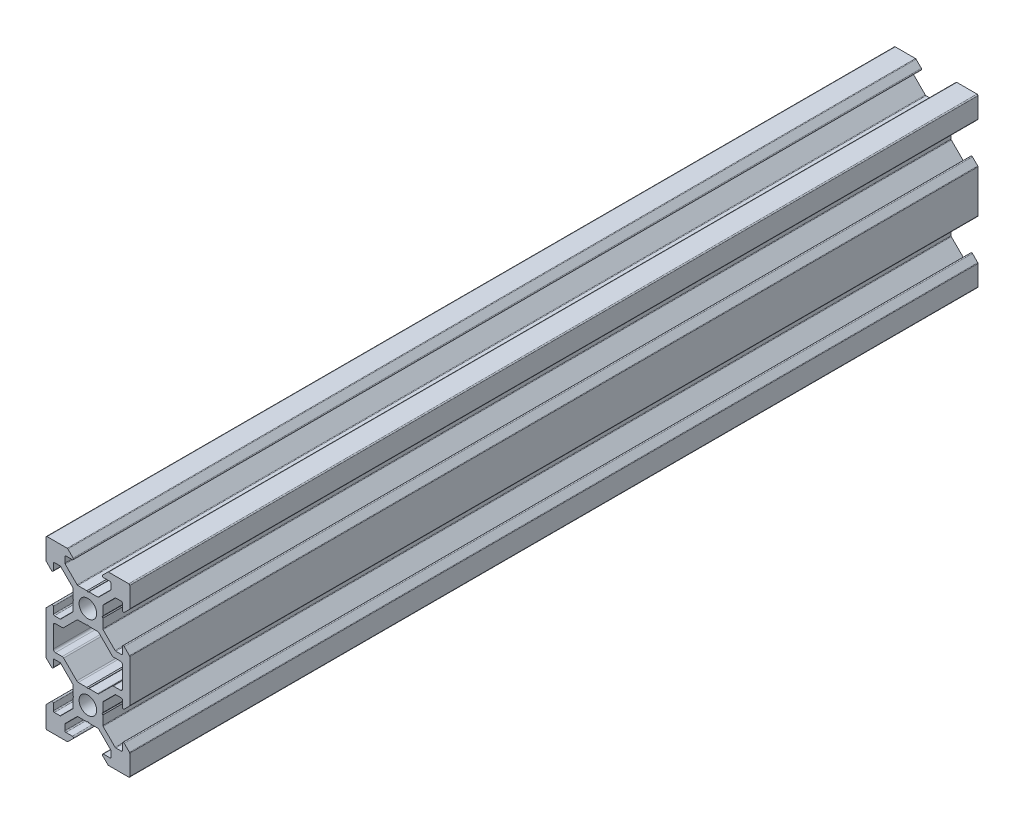
SolidWorks part; units mm, degrees
ref_plane "Front Plane" through (0, 0, 0) normal (0, 0, 1) x (1, 0, 0)
ref_plane "Top Plane" through (0, 0, 0) normal (0, 1, 0) x (1, 0, 0)
ref_plane "Right Plane" through (0, 0, 0) normal (1, 0, 0) x (0, 0, -1)
sketch "Sketch1" plane through (0, 0, 0) normal (0, 0, 1) x (1, 0, 0)
  line L0 (3.5607, 3.5607) -> (10.6317, 10.6317) construction
  line L1 (2.5, -3.5607) -> (-2.5, -3.5607)
  line L2 (3.5607, -2.5) -> (3.5607, 2.5)
  line L3 (2.5, 3.5607) -> (-2.5, 3.5607)
  line L4 (-3.5607, -2.5) -> (-3.5607, 2.5)
  line L5 (3.5607, -3.5607) -> (-3.5607, 3.5607) construction
  line L6 (3.5607, 3.5607) -> (-3.5607, -3.5607) construction
  line L7 (2.5, 3.5607) -> (5.5, 6.5607)
  line L8 (5.5, 6.5607) -> (5.5, 8.2521)
  line L9 (5.5, 8.2521) -> (3.1, 8.2521)
  line L10 (3.1, 8.2521) -> (4.8479, 10)
  line L11 (4.8479, 10) -> (10, 10)
  line L12 (3.5607, 2.5) -> (6.5607, 5.5)
  line L13 (6.5607, 5.5) -> (8.2521, 5.5)
  line L14 (8.2521, 5.5) -> (8.2521, 3.1)
  line L15 (8.2521, 3.1) -> (10, 4.8479)
  line L16 (10, 4.8479) -> (10, 10)
  line L17 (0, -55) -> (0, 55) construction
  line L18 (-3.5607, 3.5607) -> (-10.6317, 10.6317) construction
  line L19 (-10, 4.8479) -> (-10, 10)
  line L20 (-8.2521, 3.1) -> (-10, 4.8479)
  line L21 (-8.2521, 5.5) -> (-8.2521, 3.1)
  line L22 (-6.5607, 5.5) -> (-8.2521, 5.5)
  line L23 (-3.5607, 2.5) -> (-6.5607, 5.5)
  line L24 (-4.8479, 10) -> (-10, 10)
  line L25 (-3.1, 8.2521) -> (-4.8479, 10)
  line L26 (-5.5, 8.2521) -> (-3.1, 8.2521)
  line L27 (-5.5, 6.5607) -> (-5.5, 8.2521)
  line L28 (-2.5, 3.5607) -> (-5.5, 6.5607)
  line L29 (-8.2521, -7) -> (-5.9393, -7)
  line L30 (55, 0) -> (-55, 0) construction
  line L31 (-3.5607, -3.5607) -> (-10.6317, -10.6317) construction
  line L32 (3.5607, -3.5607) -> (10.6317, -10.6317) construction
  line L33 (-2.5, -3.5607) -> (-5.5, -6.5607)
  line L34 (-5.5, -6.5607) -> (-5.9393, -7)
  line L35 (5.5, -6.5607) -> (5.9393, -7)
  line L36 (8.2521, -7) -> (5.9393, -7)
  line L37 (-12.2633, -10) -> (14.5346, -10) construction
  line L38 (-3.5607, -2.5) -> (-6.5607, -5.5)
  line L39 (-6.5607, -5.5) -> (-8.2521, -5.5)
  line L40 (-8.2521, -5.5) -> (-8.2521, -3.1)
  line L41 (-8.2521, -3.1) -> (-10, -4.8479)
  line L42 (-10, -4.8479) -> (-10, -7)
  line L43 (10, -4.8479) -> (10, -7)
  line L44 (8.2521, -3.1) -> (10, -4.8479)
  line L45 (8.2521, -5.5) -> (8.2521, -3.1)
  line L46 (6.5607, -5.5) -> (8.2521, -5.5)
  line L47 (3.5607, -2.5) -> (6.5607, -5.5)
  line L48 (-3.5607, -23.5607) -> (-10.6317, -30.6317) construction
  line L49 (3.5607, -23.5607) -> (-3.5607, -16.4393) construction
  line L50 (3.5607, -16.4393) -> (-3.5607, -23.5607) construction
  line L51 (3.5607, -23.5607) -> (10.6317, -30.6317) construction
  line L52 (2.5, -3.5607) -> (5.5, -6.5607)
  line L53 (2.5, -16.4393) -> (5.5, -13.4393)
  line L54 (3.5607, -17.5) -> (6.5607, -14.5)
  line L55 (6.5607, -14.5) -> (8.2521, -14.5)
  line L56 (8.2521, -14.5) -> (8.2521, -16.9)
  line L57 (8.2521, -16.9) -> (10, -15.1521)
  line L58 (10, -15.1521) -> (10, -13)
  line L59 (-10, -15.1521) -> (-10, -13)
  line L60 (-8.2521, -16.9) -> (-10, -15.1521)
  line L61 (-8.2521, -14.5) -> (-8.2521, -16.9)
  line L62 (-6.5607, -14.5) -> (-8.2521, -14.5)
  line L63 (-3.5607, -17.5) -> (-6.5607, -14.5)
  line L64 (8.2521, -13) -> (5.9393, -13)
  line L65 (5.5, -13.4393) -> (5.9393, -13)
  line L66 (-5.5, -13.4393) -> (-5.9393, -13)
  line L67 (-2.5, -16.4393) -> (-5.5, -13.4393)
  line L68 (-8.2521, -13) -> (-5.9393, -13)
  line L69 (-2.5, -23.5607) -> (-5.5, -26.5607)
  line L70 (-5.5, -26.5607) -> (-5.5, -28.2521)
  line L71 (-5.5, -28.2521) -> (-3.1, -28.2521)
  line L72 (-3.1, -28.2521) -> (-4.8479, -30)
  line L73 (-4.8479, -30) -> (-10, -30)
  line L74 (-3.5607, -22.5) -> (-6.5607, -25.5)
  line L75 (-6.5607, -25.5) -> (-8.2521, -25.5)
  line L76 (-8.2521, -25.5) -> (-8.2521, -23.1)
  line L77 (-8.2521, -23.1) -> (-10, -24.8479)
  line L78 (-10, -24.8479) -> (-10, -30)
  line L79 (10, -24.8479) -> (10, -30)
  line L80 (8.2521, -23.1) -> (10, -24.8479)
  line L81 (8.2521, -25.5) -> (8.2521, -23.1)
  line L82 (6.5607, -25.5) -> (8.2521, -25.5)
  line L83 (3.5607, -22.5) -> (6.5607, -25.5)
  line L84 (4.8479, -30) -> (10, -30)
  line L85 (3.1, -28.2521) -> (4.8479, -30)
  line L86 (5.5, -28.2521) -> (3.1, -28.2521)
  line L87 (5.5, -26.5607) -> (5.5, -28.2521)
  line L88 (2.5, -23.5607) -> (5.5, -26.5607)
  line L89 (-3.5607, -17.5) -> (-3.5607, -22.5)
  line L90 (2.5, -23.5607) -> (-2.5, -23.5607)
  line L91 (3.5607, -17.5) -> (3.5607, -22.5)
  line L92 (2.5, -16.4393) -> (-2.5, -16.4393)
  line L93 (-10, -7) -> (-10, -13)
  line L94 (-8.2521, -13) -> (-8.2521, -7)
  line L95 (8.2521, -13) -> (8.2521, -7)
  line L96 (10, -7) -> (10, -13)
  circle A0 centre (0, 0) radius 2.1
  circle A1 centre (0, -20) radius 2.1
  point P0 (0, 0)
  point P102 (0, -20)
  dimension "D10" = 4.2
  dimension "D11" = 4.2
  dimension "D1" = 1.5
  dimension "D2" = 10
  dimension "D3" = 20
  dimension "D4" = 6.2
  dimension "D5" = 11
  dimension "D6" = 45
  dimension "D7" = 1.5
  dimension "D8" = 10
  dimension "D9" = 5
extrude "Boss-Extrude1" add sketch "Sketch1" along normal blind 202.56
fillet "Fillet1" radius 0.25 64 edges at (5.5, 6.5607, 101.28) (5.5, 8.2521, 101.28) (3.1, 8.2521, 101.28) (4.8479, 10, 101.28) (10, 10, 101.28) (10, 4.8479, 101.28) (8.2521, 3.1, 101.28) (8.2521, 5.5, 101.28) (6.5607, 5.5, 101.28) (3.5607, 2.5, 101.28) (3.5607, -2.5, 101.28) (6.5607, -5.5, 101.28) (8.2521, -5.5, 101.28) (8.2521, -3.1, 101.28) (10, -4.8479, 101.28) (10, -15.1521, 101.28) (8.2521, -16.9, 101.28) (8.2521, -14.5, 101.28) (6.5607, -14.5, 101.28) (3.5607, -17.5, 101.28) (3.5607, -22.5, 101.28) (6.5607, -25.5, 101.28) (8.2521, -25.5, 101.28) (8.2521, -23.1, 101.28) (10, -24.8479, 101.28) (10, -30, 101.28) (4.8479, -30, 101.28) (3.1, -28.2521, 101.28) (5.5, -28.2521, 101.28) (5.5, -26.5607, 101.28) (2.5, -23.5607, 101.28) (-2.5, -23.5607, 101.28) (-5.5, -26.5607, 101.28) (-5.5, -28.2521, 101.28) (-3.1, -28.2521, 101.28) (-4.8479, -30, 101.28) (-10, -30, 101.28) (-10, -24.8479, 101.28) (-8.2521, -23.1, 101.28) (-8.2521, -25.5, 101.28) (-6.5607, -25.5, 101.28) (-3.5607, -22.5, 101.28) (-3.5607, -17.5, 101.28) (-6.5607, -14.5, 101.28) (-8.2521, -14.5, 101.28) (-8.2521, -16.9, 101.28) (-10, -15.1521, 101.28) (-10, -4.8479, 101.28) (-8.2521, -3.1, 101.28) (-8.2521, -5.5, 101.28) (-6.5607, -5.5, 101.28) (-3.5607, -2.5, 101.28) (-3.5607, 2.5, 101.28) (-6.5607, 5.5, 101.28) (-8.2521, 5.5, 101.28) (-8.2521, 3.1, 101.28) (-10, 4.8479, 101.28) (-10, 10, 101.28) (-4.8479, 10, 101.28) (-5.5, 8.2521, 101.28) (-5.5, 6.5607, 101.28) (-2.5, 3.5607, 101.28) (2.5, 3.5607, 101.28) (-3.1, 8.2521, 101.28)
fillet "Fillet2" radius 0.5 12 edges at (-5.9393, -7, 101.28) (-8.2521, -7, 101.28) (-8.2521, -13, 101.28) (-5.9393, -13, 101.28) (-2.5, -16.4393, 101.28) (2.5, -16.4393, 101.28) (8.2521, -7, 101.28) (5.9393, -7, 101.28) (2.5, -3.5607, 101.28) (-2.5, -3.5607, 101.28) (5.9393, -13, 101.28) (8.2521, -13, 101.28)
sketch "Sketch2" plane through (0, 0, 202.56) normal (0, 0, 1) x (1, 0, 0)
  line L4 (0, 3.5607) -> (0, 3.1447) construction
  line L5 (2.3964, 3.5607) -> (-2.3964, 3.5607) construction
  line L6 (0, 3.399) -> (-0.2423, 3.5607)
  line L7 (0, 3.399) -> (0.2423, 3.5607)
  line L8 (-0.2423, 3.5607) -> (0.2423, 3.5607)
  line L9 (55, 0) -> (-55, 0) construction
  line L10 (0, -3.5607) -> (0, -3.1447) construction
  line L11 (0, -3.399) -> (0.2423, -3.5607)
  line L12 (0, -3.399) -> (-0.2423, -3.5607)
  line L13 (-0.2423, -3.5607) -> (0.2423, -3.5607)
  line L14 (0, 0) -> (-4.0856, 4.0856) construction
  line L15 (-8.2521, -10) -> (4.1581, -10) construction
  line L16 (-8.2521, -7.5) -> (-8.2521, -12.5) construction
  line L17 (3.5607, 0) -> (3.1447, 0) construction
  line L18 (3.5607, 0.2423) -> (3.5607, -0.2423)
  line L19 (3.399, 0) -> (3.5607, 0.2423)
  line L20 (3.399, 0) -> (3.5607, -0.2423)
  line L21 (-3.5607, 0) -> (-3.1447, 0) construction
  line L22 (-3.5607, 0.2423) -> (-3.5607, -0.2423)
  line L23 (-3.399, 0) -> (-3.5607, -0.2423)
  line L24 (-3.399, 0) -> (-3.5607, 0.2423)
  line L25 (-3.5607, -20) -> (-3.1447, -20) construction
  line L26 (3.5607, -20) -> (3.1447, -20) construction
  line L27 (0, -20) -> (-4.0856, -24.0856) construction
  line L28 (0, -16.4393) -> (0, -16.8553) construction
  line L29 (0, -23.5607) -> (0, -23.1447) construction
  line L30 (-3.399, -20) -> (-3.5607, -20.2423)
  line L31 (-3.399, -20) -> (-3.5607, -19.7577)
  line L32 (-3.5607, -20.2423) -> (-3.5607, -19.7577)
  line L33 (3.399, -20) -> (3.5607, -19.7577)
  line L34 (3.399, -20) -> (3.5607, -20.2423)
  line L35 (3.5607, -20.2423) -> (3.5607, -19.7577)
  line L36 (-0.2423, -16.4393) -> (0.2423, -16.4393)
  line L37 (0, -16.601) -> (-0.2423, -16.4393)
  line L38 (0, -16.601) -> (0.2423, -16.4393)
  line L39 (-0.2423, -23.5607) -> (0.2423, -23.5607)
  line L40 (0, -23.399) -> (0.2423, -23.5607)
  line L41 (0, -23.399) -> (-0.2423, -23.5607)
extrude "Cut-Extrude1" cut sketch "Sketch2" against normal through all
